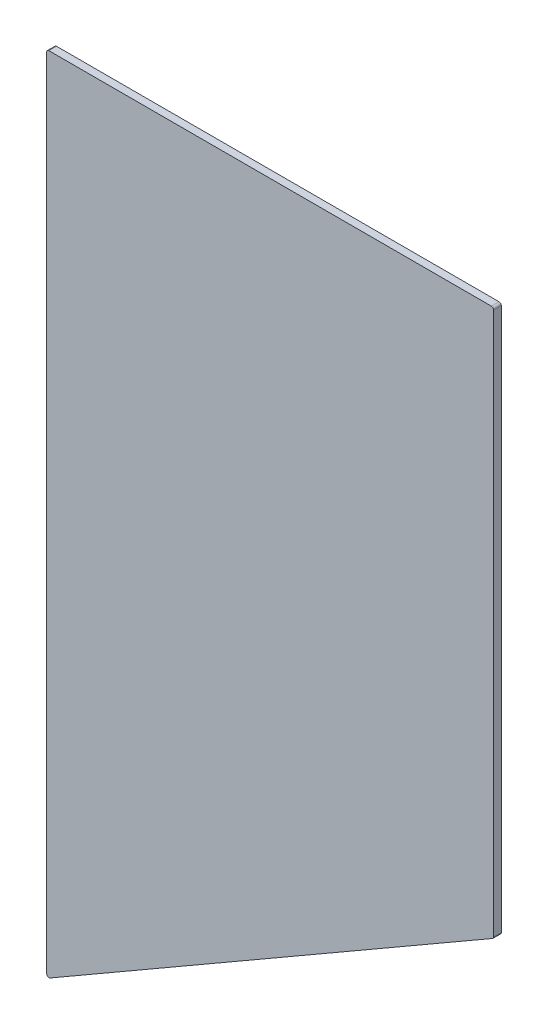
SolidWorks part; units mm, degrees
ref_plane "Front Plane" through (0, 0, 0) normal (0, 0, 1) x (1, 0, 0)
ref_plane "Top Plane" through (0, 0, 0) normal (0, 1, 0) x (1, 0, 0)
ref_plane "Right Plane" through (0, 0, 0) normal (1, 0, 0) x (0, 0, -1)
sketch "Sketch1" plane through (0, 0, 0) normal (0, 0, 1) x (1, 0, 0)
  line L1 (-127, -228.6) -> (127, -228.6)
  line L2 (-127, -228.6) -> (-127, 228.6)
  line L3 (-127, 228.6) -> (127, 228.6)
  line L4 (127, -228.6) -> (127, 228.6)
  line L5 (-127, -228.6) -> (127, 228.6) construction
  line L6 (-127, 228.6) -> (127, -228.6) construction
  point P0 (0, 0)
  dimension "D1" = 254
  dimension "D2" = 457.2
extrude "Boss-Extrude1" add sketch "Sketch1" along normal blind 4.3434
sketch "Sketch4" plane through (0, 0, 4.3434) normal (0, 0, 1) x (1, 0, 0)
  line L0 (-127, -228.6) -> (127, -81.953)
  line L1 (127, -228.6) -> (127, 228.6) construction
  line L2 (127, -81.953) -> (127, -228.6)
  line L3 (127, -228.6) -> (-127, -228.6)
  line L4 (-127, 228.6) -> (-127, -228.6) construction
  dimension "D1" = 60
extrude "Cut-Extrude3" cut sketch "Sketch4" against normal through all
fillet "Fillet2" radius 1.27 4 edges at (-127, 228.6, 2.1717) (-127, -228.6, 2.1717) (127, -81.953, 2.1717) (127, 228.6, 2.1717)
